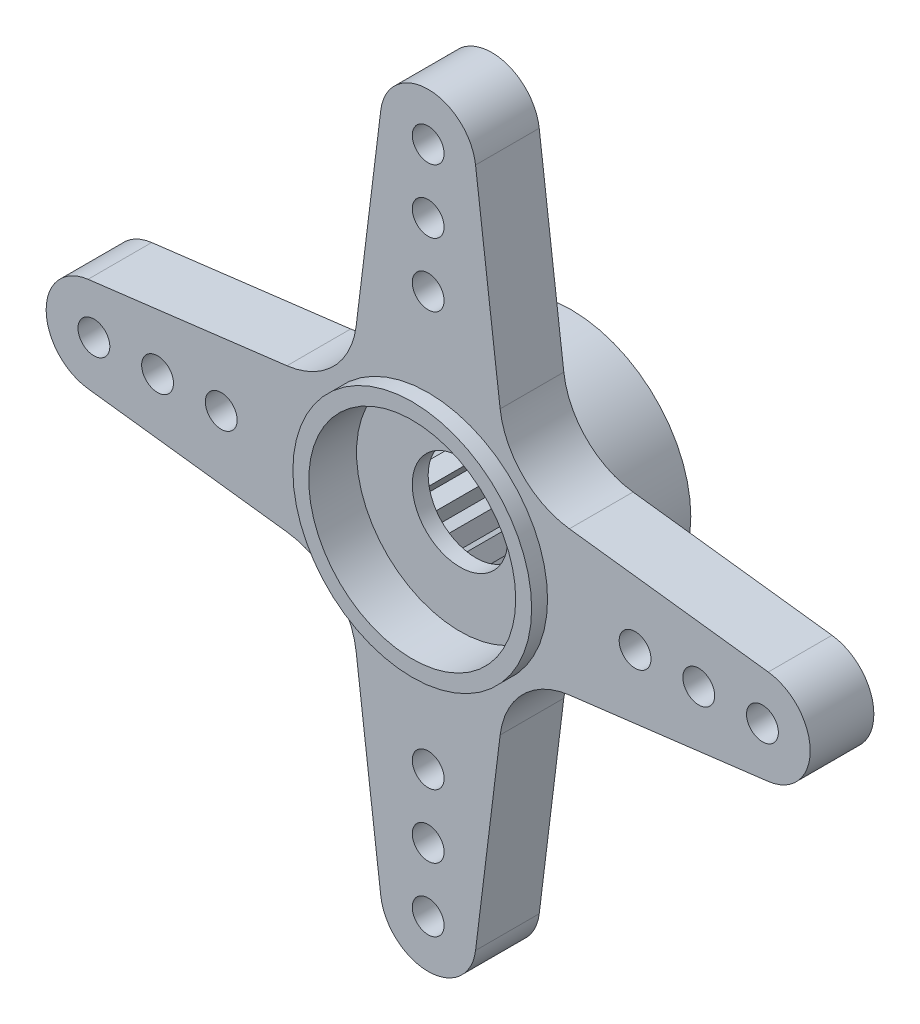
SolidWorks part; units mm, degrees
material "Nylon 101"
ref_plane "Plan1" through (0, 0, 0) normal (0, 0, 1) x (1, 0, 0)
ref_plane "Plan2" through (0, 0, 0) normal (0, 1, 0) x (1, 0, 0)
ref_plane "Plan3" through (0, 0, 0) normal (1, 0, 0) x (0, 0, -1)
sketch "Esquisse1" plane through (0, 0, 0) normal (0, 0, 1) x (1, 0, 0)
  line L0 (0, 60) -> (0, -60) construction
  line L1 (1.4887, 10.684) -> (2.2608, 4.4354)
  line L2 (-28.118, 0) -> (45.118, 0) construction
  line L3 (4.4354, 2.2608) -> (10.684, 1.4887)
  line L4 (-4.4354, 2.2608) -> (-10.684, 1.4887)
  line L5 (-1.4887, 10.684) -> (-2.2608, 4.4354)
  line L6 (-1.4887, -10.684) -> (-2.2608, -4.4354)
  line L7 (-4.4354, -2.2608) -> (-10.684, -1.4887)
  line L8 (4.4354, -2.2608) -> (10.684, -1.4887)
  line L9 (1.4887, -10.684) -> (2.2608, -4.4354)
  line L10 (0, 0) -> (24.5169, -24.5169) construction
  arc A0 (1.4887, 10.684) -> (-1.4887, 10.684) centre (0, 10.5) ccw
  arc A1 (10.684, -1.4887) -> (10.684, 1.4887) centre (10.5, 0) ccw
  arc A2 (4.4354, 2.2608) -> (2.2608, 4.4354) centre (4.742, 4.742) cw
  arc A3 (-4.4354, 2.2608) -> (-2.2608, 4.4354) centre (-4.742, 4.742) ccw
  arc A4 (-10.684, -1.4887) -> (-10.684, 1.4887) centre (-10.5, 0) cw
  arc A5 (-4.4354, -2.2608) -> (-2.2608, -4.4354) centre (-4.742, -4.742) cw
  arc A6 (4.4354, -2.2608) -> (2.2608, -4.4354) centre (4.742, -4.742) ccw
  arc A7 (1.4887, -10.684) -> (-1.4887, -10.684) centre (0, -10.5) cw
  circle A8 centre (10.5, 0) radius 0.5
  circle A9 centre (8.5, 0) radius 0.5
  circle A10 centre (6.5, 0) radius 0.5
  circle A11 centre (0, -10.5) radius 0.5
  circle A12 centre (0, -8.5) radius 0.5
  circle A13 centre (0, -6.5) radius 0.5
  circle A14 centre (0, 10.5) radius 0.5
  circle A15 centre (0, 8.5) radius 0.5
  circle A16 centre (0, 6.5) radius 0.5
  circle A17 centre (-10.5, 0) radius 0.5
  circle A18 centre (-8.5, 0) radius 0.5
  circle A19 centre (-6.5, 0) radius 0.5
  point P16 (2.5, 2.5)
  dimension "D1" = 3
  dimension "D5" = 3
  dimension "D7" = 2.5
  dimension "D8" = 1
  dimension "D3" = 2.5
  dimension "D4" = 2.5
  dimension "D6" = 10.5
  dimension "D10" = 2
  dimension "D11" = 2
extrude "Base-Extrusion" add sketch "Esquisse1" along normal mid plane 2
sketch "Esquisse2" plane through (0, 0, 1) normal (0, 0, 1) x (1, 0, 0)
  circle A0 centre (0, 0) radius 3.75
  dimension "D1" = 7.5
extrude "Boss.-Extru.1" add sketch "Esquisse2" along normal blind 0.5
sketch "Esquisse3" plane through (0, 0, -1) normal (0, 0, -1) x (-1, 0, 0)
  circle A0 centre (0, 0) radius 3.75 construction
  circle A1 centre (0, 0) radius 3.75
extrude "Boss.-Extru.2" add sketch "Esquisse3" along normal blind 2.5
sketch "Esquisse4" plane through (0, 0, 1.5) normal (0, 0, 1) x (1, 0, 0)
  circle A0 centre (0, 0) radius 3.25
  circle A1 centre (0, 0) radius 3.75 construction
  dimension "D1" = 6.5
extrude "Enlèv. mat.-Extru.1" cut sketch "Esquisse4" against normal blind 1.5
sketch "Esquisse5" plane through (0, 0, 0) normal (0, 0, 1) x (1, 0, 0)
  circle A0 centre (0, 0) radius 1.5
  circle A1 centre (0, 0) radius 3.75 construction
  dimension "D1" = 3
extrude "Enlèv. mat.-Extru.2" cut sketch "Esquisse5" against normal through all
sketch "Esquisse7" plane through (0, 0, -3.5) normal (0, 0, -1) x (-1, 0, 0)
  circle A0 centre (0, 0) radius 2.2
  circle A1 centre (0, 0) radius 3.75 construction
  dimension "D1" = 4.4
extrude "Enlèv. mat.-Extru.4" cut sketch "Esquisse7" against normal blind 3
sketch "Esquisse6" plane through (0, 0, -3.5) normal (0, 0, -1) x (-1, 0, 0)
  line L0 (0, 0) -> (0, 12.8926) construction
  line L1 (0, 2.8) -> (0.2887, 2.181)
  line L2 (0, 2.8) -> (-0.2887, 2.181)
  line L3 (0, 0) -> (0.4308, 3.2725) construction
  circle A0 centre (0, 0) radius 2.2 construction
  arc A2 (0.2887, 2.181) -> (-0.2887, 2.181) centre (0, 0) ccw
  dimension "D2" = 2.8
  dimension "D4" = 7.5
  dimension "D5" = 25
extrude "Dents" cut sketch "Esquisse6" against normal blind 3
pattern_circular "Répétition circulaire1" count 24 over 360 about axis through (0, 0, 0) along (0, 0, 1) of "Dents"
sketch "Esquisse9" plane through (0, 0, 1) normal (0, 0, 1) x (1, 0, 0)
  line L0 (0, 0) -> (0, 13.0493) construction
